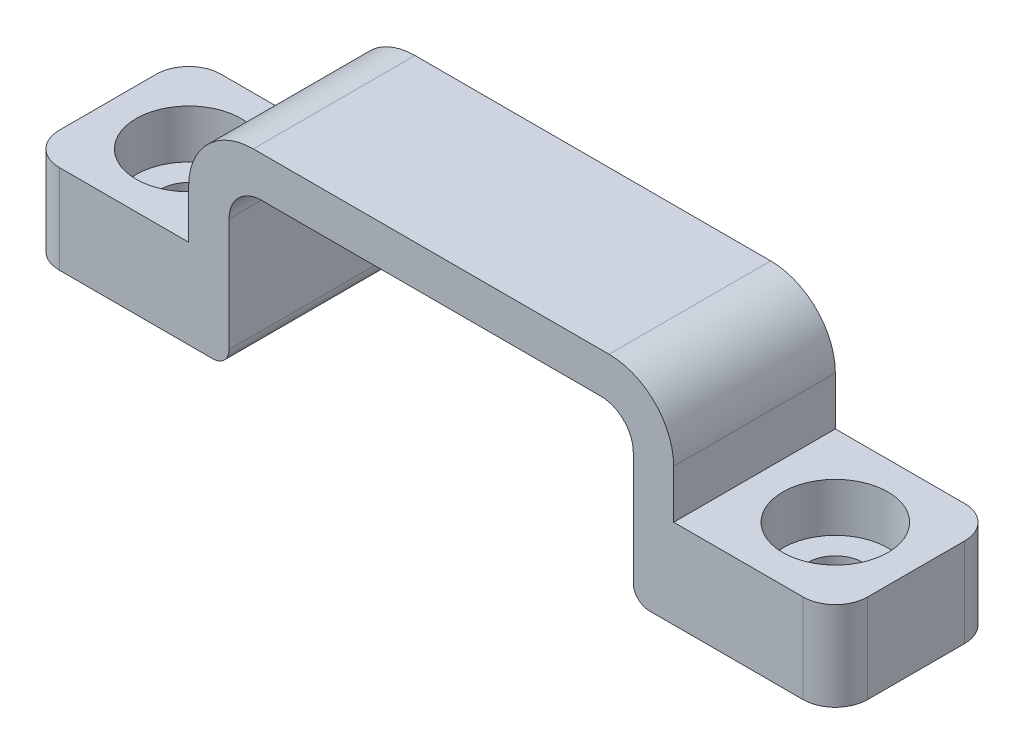
SolidWorks part; units mm, degrees
ref_plane "Front Plane" through (0, 0, 0) normal (0, 0, 1) x (1, 0, 0)
ref_plane "Top Plane" through (0, 0, 0) normal (0, 1, 0) x (1, 0, 0)
ref_plane "Right Plane" through (0, 0, 0) normal (1, 0, 0) x (0, 0, -1)
sketch "Sketch1" plane through (0, 0, 0) normal (0, 0, 1) x (1, 0, 0)
  line L0 (-15, 2.5) -> (15, 2.5)
  line L1 (15, 2.5) -> (15, -4.5)
  line L2 (15, -10) -> (12.5, -10)
  line L3 (12.5, -10) -> (12.5, 0)
  line L8 (0, 0) -> (0, 16.5989) construction
  line L9 (-12.5, 0) -> (12.5, 0)
  line L10 (15, -4.5) -> (25, -4.5)
  line L12 (15, -10) -> (25, -10)
  line L13 (25, -4.5) -> (25, -10)
  line L14 (20, -4.5) -> (20, -10) construction
  line L15 (-20, -4.5) -> (-20, -10) construction
  line L16 (-25, -4.5) -> (-25, -10)
  line L17 (-15, -10) -> (-25, -10)
  line L18 (-15, -4.5) -> (-25, -4.5)
  line L19 (-12.5, -10) -> (-12.5, 0)
  line L20 (-15, -10) -> (-12.5, -10)
  line L21 (-15, 2.5) -> (-15, -4.5)
  point P22 (0, 2.5)
  dimension "D5" = 2.5
  dimension "D6" = 5.5
  dimension "D7" = 10
  dimension "D1" = 2.5
  dimension "D2" = 40
  dimension "D3" = 10
extrude "Boss-Extrude1" add sketch "Sketch1" along normal mid plane 10
fillet "Fillet1" radius 2 2 edges at (12.5, 0, 0) (-12.5, 0, 0)
fillet "Fillet2" radius 4 2 edges at (-15, 2.5, 0) (15, 2.5, 0)
fillet "Fillet3" radius 2 4 edges at (-25, -7.25, -5) (-25, -7.25, 5) (25, -7.25, -5) (25, -7.25, 5)
fillet "Fillet4" radius 1 2 edges at (-12.5, -10, 0) (12.5, -10, 0)
sketch "Sketch5" plane through (0, -4.5, 0) normal (0, 1, 0) x (1, 0, 0)
  line L0 (-25, 0) -> (-15, 0) construction
  line L1 (-25, -3) -> (-25, 3) construction
  line L3 (15, 0) -> (25, 0) construction
  line L5 (25, -3) -> (25, 3) construction
  line L7 (15, -5) -> (15, 5) construction
  line L8 (-15, -5) -> (-15, 5) construction
  point P12 (-20, 0)
  point P13 (20, 0)
  point P15 (0, 0)
  point P18 (0, 0)
  point P19 (0, 0)
hole_wizard "CBORE for M3 SHCS2" positions "Sketch5" profile "Sketch6" counterbore size "M3" standard "ANSI Metric" end condition through all
sketch "Sketch6" plane through (20, -4.5, 0) normal (1, 0, 0) x (0, 0, 1)
  line L0 (0, 0) -> (0, 5.5)
  line L1 (0, 5.5) -> (1.7, 5.5)
  line L3 (1.7, 5.5) -> (1.7, 3)
  line L4 (1.7, 3) -> (3.25, 3)
  line L5 (3.25, 3) -> (3.25, 0)
  line L7 (3.25, 0) -> (0, 0)
  line L11 (0, -6.35) -> (0, 107.95) construction
  dimension "Thru Hole Dia." = 3.4
  dimension "Thru Hole Depth" = 5.5
  dimension "C'Bore Dia." = 6.5
  dimension "C'Bore Depth" = 3
equation "\"D1@Sketch1\"=\"D5@Sketch1\""
